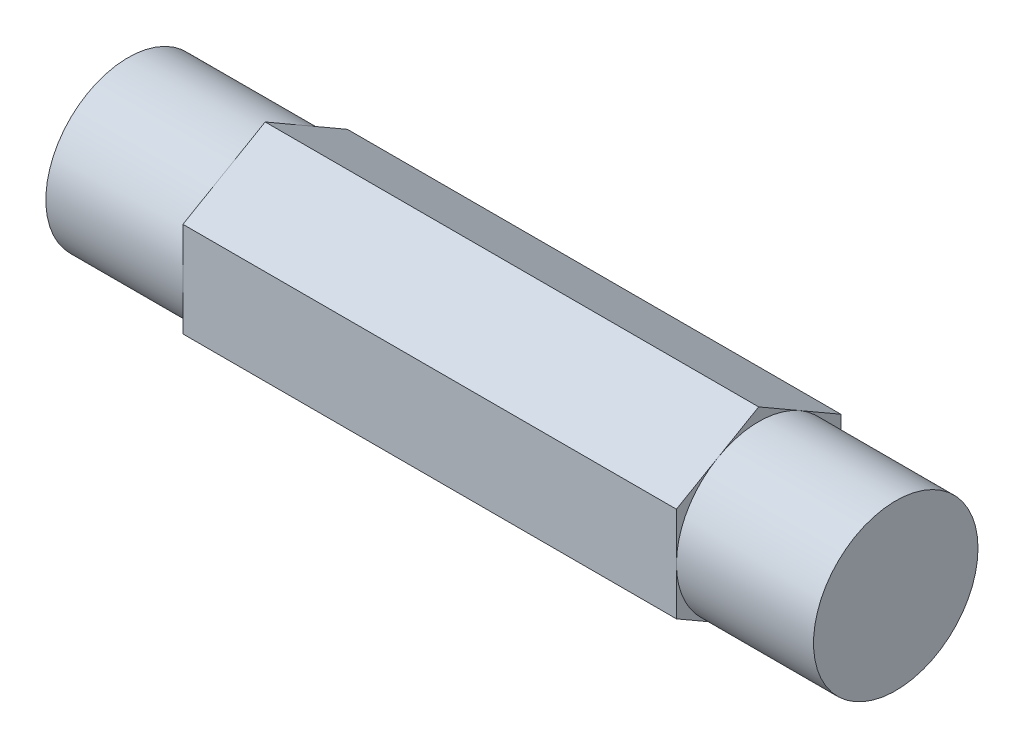
SolidWorks part; units mm, degrees
material "7075-T6 (SN)"
ref_plane "Front Plane" through (0, 0, 0) normal (0, 0, 1) x (1, 0, 0)
ref_plane "Top Plane" through (0, 0, 0) normal (0, 1, 0) x (1, 0, 0)
ref_plane "Right Plane" through (0, 0, 0) normal (1, 0, 0) x (0, 0, -1)
sketch "Sketch1" plane through (0, 0, 0) normal (1, 0, 0) x (0, 0, -1)
  line L1 (0, 5.4993) -> (-4.7625, 2.7496)
  line L2 (-4.7625, 2.7496) -> (-4.7625, -2.7496)
  line L3 (-4.7625, -2.7496) -> (0, -5.4993)
  line L4 (0, -5.4993) -> (4.7625, -2.7496)
  line L5 (4.7625, -2.7496) -> (4.7625, 2.7496)
  line L6 (4.7625, 2.7496) -> (0, 5.4993)
  circle A1 centre (0, 0) radius 4.7625 construction
  dimension "D1" = 9.525
extrude "Boss-Extrude1" add sketch "Sketch1" along normal blind 44.45
sketch "Sketch2" plane through (0, 0, 0) normal (-1, 0, 0) x (0, 0, 1)
  line L0 (0, -5.4993) -> (-4.7625, -2.7496) construction
  circle A0 centre (0, 0) radius 4.7625
  circle A1 centre (0, 0) radius 5.4993
extrude "Cut-Extrude1" cut sketch "Sketch2" against normal blind 7.9375
sketch "Sketch3" plane through (44.45, 0, 0) normal (1, 0, 0) x (0, 0, -1)
  line L0 (4.7625, -2.7496) -> (4.7625, 2.7496) construction
  circle A0 centre (0, 0) radius 4.7625
  circle A1 centre (0, 0) radius 5.4993
extrude "Cut-Extrude2" cut sketch "Sketch3" against normal blind 7.9375
